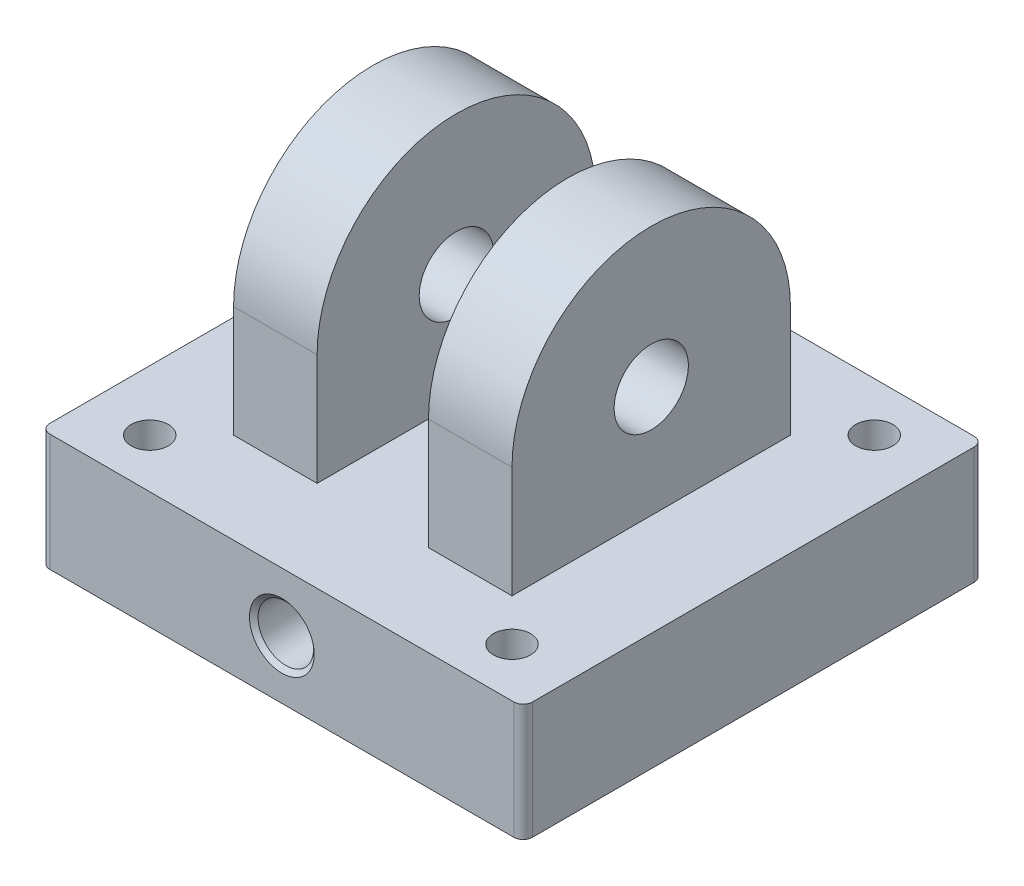
SolidWorks part; units mm, degrees
ref_plane "Front Plane" through (0, 0, 0) normal (0, 0, 1) x (1, 0, 0)
ref_plane "Top Plane" through (0, 0, 0) normal (0, 1, 0) x (1, 0, 0)
ref_plane "Right Plane" through (0, 0, 0) normal (1, 0, 0) x (0, 0, -1)
sketch "Sketch1" plane through (0, 0, 0) normal (0, 1, 0) x (1, 0, 0)
  line L1 (-82.55, 78.7347) -> (82.55, 78.7347)
  line L2 (-82.55, 78.7347) -> (-82.55, -78.7347)
  line L3 (-82.55, -78.7347) -> (82.55, -78.7347)
  line L4 (82.55, 78.7347) -> (82.55, -78.7347)
  line L5 (-82.55, 78.7347) -> (82.55, -78.7347) construction
  line L6 (-82.55, -78.7347) -> (82.55, 78.7347) construction
  point P0 (0, 0)
  dimension "D1" = 165.1
extrude "Boss-Extrude1" add sketch "Sketch1" along normal blind 38.1 and the other way blind 2
sketch "Sketch2" plane through (0, 38.1, 0) normal (0, 1, 0) x (1, 0, 0)
  line L1 (-47.625, 47.625) -> (47.625, 47.625)
  line L2 (-47.625, 47.625) -> (-47.625, -47.625)
  line L3 (-47.625, -47.625) -> (47.625, -47.625)
  line L4 (47.625, 47.625) -> (47.625, -47.625)
  line L5 (-47.625, 47.625) -> (47.625, -47.625) construction
  line L6 (-47.625, -47.625) -> (47.625, 47.625) construction
  point P0 (0, 0)
  dimension "D1" = 95.25
extrude "Boss-Extrude2" add sketch "Sketch2" along normal blind 38.1
sketch "Sketch3" plane through (-47.625, 0, 0) normal (-1, 0, 0) x (0, 0, 1)
  line L0 (-47.625, 76.2) -> (47.625, 76.2)
  arc A0 (-47.625, 76.2) -> (47.625, 76.2) centre (0, 76.2) cw
extrude "Boss-Extrude3" add sketch "Sketch3" against normal up to vertex
sketch "Sketch4" plane through (-47.625, 0, 0) normal (-1, 0, 0) x (0, 0, 1)
  circle A0 centre (0, 76.2) radius 12.7
  dimension "D1" = 25.4
extrude "Cut-Extrude1" cut sketch "Sketch4" against normal through all
sketch "Sketch5" plane through (0, 0, 47.625) normal (0, 0, 1) x (1, 0, 0)
  line L0 (-47.625, 38.1) -> (47.625, 38.1) construction
  line L1 (-19.05, 38.1) -> (19.05, 38.1)
  line L2 (-19.05, 38.1) -> (-19.05, 123.825)
  line L3 (-19.05, 123.825) -> (19.05, 123.825)
  line L4 (19.05, 38.1) -> (19.05, 123.825)
  line L5 (47.625, 123.825) -> (-47.625, 123.825) construction
  dimension "D1" = 28.575
  dimension "D2" = 38.1
extrude "Cut-Extrude3" cut sketch "Sketch5" against normal through all
fillet "Fillet1" radius 3.175 4 edges at (82.55, 18.05, -78.7347) (-82.55, 18.05, 78.7347) (-82.55, 18.05, -78.7347) (82.55, 18.05, 78.7347)
sketch "Sketch6" plane through (0, -2, 0) normal (0, -1, 0) x (1, 0, 0)
  circle A0 centre (0, 0) radius 26
  dimension "D1" = 52
extrude "Cut-Extrude4" cut sketch "Sketch6" against normal blind 36.83
sketch "Sketch9" plane through (0, -2, 0) normal (0, -1, 0) x (1, 0, 0)
  circle A0 centre (0, 0) radius 69.85
  circle A1 centre (0, 0) radius 76.2
  dimension "D1" = 152.4
  dimension "D2" = 139.7
extrude "Cut-Extrude5" cut sketch "Sketch9" against normal blind 8
sketch "Sketch10" plane through (0, 0, 78.7347) normal (0, 0, 1) x (1, 0, 0)
  line L0 (-79.375, 18.05) -> (79.375, 18.05) construction
  line L1 (-79.375, 38.1) -> (-79.375, -2) construction
  line L2 (79.375, -2) -> (79.375, 38.1) construction
sketch "Sketch13" plane through (0, 0, 78.7347) normal (0, 0, 1) x (1, 0, 0)
  line L0 (0, 23.1055) -> (0, 14.2098) construction
hole_wizard "1/2-14 NPSM Tapped Hole1" positions "Sketch14" profile "Sketch15" tap size "1/2-14 NPSM" standard "ANSI Inch"
sketch "Sketch14" plane through (0, 0, 78.7347) normal (0, 0, 1) x (1, 0, 0)
  line L0 (-79.375, 18.05) -> (79.375, 18.05) construction
  point P0 (0, 18.05)
sketch "Sketch15" plane through (0, 18.05, 78.7347) normal (1, 0, 0) x (0, -1, 0)
  line L0 (0, 0) -> (0, 69.2003)
  line L1 (0, 69.2003) -> (9.4869, 63.5)
  line L2 (9.4869, 63.5) -> (9.4869, 1.3427)
  line L3 (9.4869, 1.3427) -> (11.0871, 0)
  line L5 (11.0871, 0) -> (0, 0)
  line L6 (-9.4869, 1.3427) -> (-11.0871, 0) construction
  line L10 (0, 69.2003) -> (-9.4869, 63.5) construction
  line L11 (0, -6.35) -> (0, 107.95) construction
  dimension "Tap Drill Dia." = 18.9738
  dimension "Tap Drill Depth" = 63.5
  dimension "Near C'Sink Dia." = 22.1742
  dimension "Near C'Sink Angle" = 100
  dimension "Drill Angle" = 118
cosmetic thread "Hole Thread1" parameters "D1"=41.91, "D2"=20.9042
sketch "Sketch16" plane through (0, -2, 0) normal (0, -1, 0) x (1, 0, 0)
  line L0 (-79.375, 78.7347) -> (79.375, 78.7347) construction
  circle A0 centre (0, 46.7347) radius 6.35
  dimension "D1" = 12.7
  dimension "D2" = 32
extrude "Cut-Extrude6" cut sketch "Sketch16" against normal blind 25
sketch "Sketch17" plane through (0, -2, 0) normal (0, -1, 0) x (1, 0, 0)
  line L1 (-61.9638, 61.9638) -> (61.9638, 61.9638) construction
  line L2 (-61.9638, 61.9638) -> (-61.9638, -61.9638) construction
  line L3 (-61.9638, -61.9638) -> (61.9638, -61.9638) construction
  line L4 (61.9638, 61.9638) -> (61.9638, -61.9638) construction
  line L5 (-61.9638, 61.9638) -> (61.9638, -61.9638) construction
  line L6 (-61.9638, -61.9638) -> (61.9638, 61.9638) construction
  circle A0 centre (0, 0) radius 87.63 construction
  circle A1 centre (-61.9638, 61.9638) radius 6.35
  circle A2 centre (61.9638, 61.9638) radius 6.35
  circle A3 centre (61.9638, -61.9638) radius 6.35
  circle A4 centre (-61.9638, -61.9638) radius 6.35
  dimension "D1" = 175.26
  dimension "D2" = 12.7
extrude "Cut-Extrude7" cut sketch "Sketch17" against normal through all
